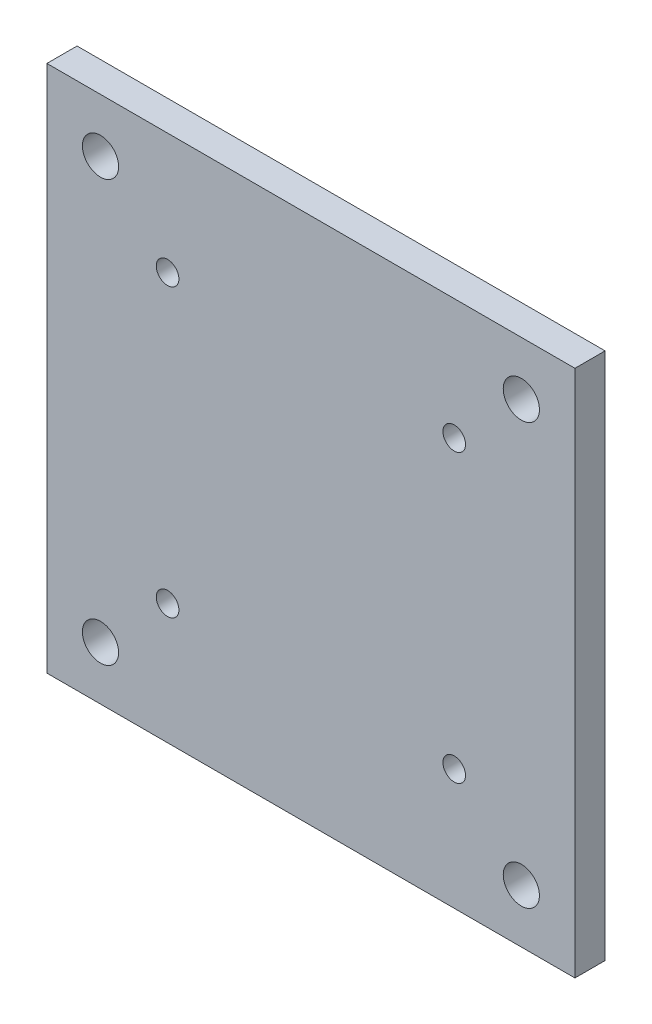
SolidWorks part; units mm, degrees
ref_plane "Front Plane" through (0, 0, 0) normal (0, 0, 1) x (1, 0, 0)
ref_plane "Top Plane" through (0, 0, 0) normal (0, 1, 0) x (1, 0, 0)
ref_plane "Right Plane" through (0, 0, 0) normal (1, 0, 0) x (0, 0, -1)
sketch "Sketch1" plane through (0, 0, 0) normal (0, 0, 1) x (1, 0, 0)
  line L0 (-35, 70) -> (35, 70)
  line L1 (0, 70) -> (0, 0) construction
  line L2 (35, 0) -> (-35, 0)
  line L3 (-27.895, 62.895) -> (-27.895, 7.105) construction
  line L5 (27.895, 7.105) -> (25.495, 7.105) construction
  line L7 (-35, 35) -> (0, 35) construction
  line L8 (-35, 70) -> (-35, 0)
  line L9 (-27.895, 7.105) -> (-25.495, 7.105) construction
  line L10 (35, 70) -> (35, 0)
  line L13 (-19, 54) -> (-19, 16) construction
  circle A0 centre (-27.895, 7.105) radius 2.4
  circle A1 centre (-27.895, 62.895) radius 2.4
  circle A2 centre (19, 54) radius 1.5
  circle A3 centre (19, 16) radius 1.5
  circle A4 centre (-19, 16) radius 1.5
  circle A5 centre (27.895, 62.895) radius 2.4
  circle A6 centre (27.895, 7.105) radius 2.4
  circle A7 centre (-19, 54) radius 1.5
  point P1 (-17.9, 53.5099)
  point P27 (0, 0)
  dimension "D2" = 4.8
  dimension "D10" = 3
  dimension "D3" = 35
  dimension "D4" = 38
  dimension "D5" = 70
  dimension "D6" = 55.79
  dimension "D7" = 16
  dimension "D8" = 19
  dimension "D9" = 27.895
  dimension "D13" = 7.105
extrude "Boss-Extrude2" add sketch "Sketch1" along normal blind 4 contours L0 L10 L2 L8 | A1 | A0 | A4 | A7 | A2 | A5 | A3 | A6
